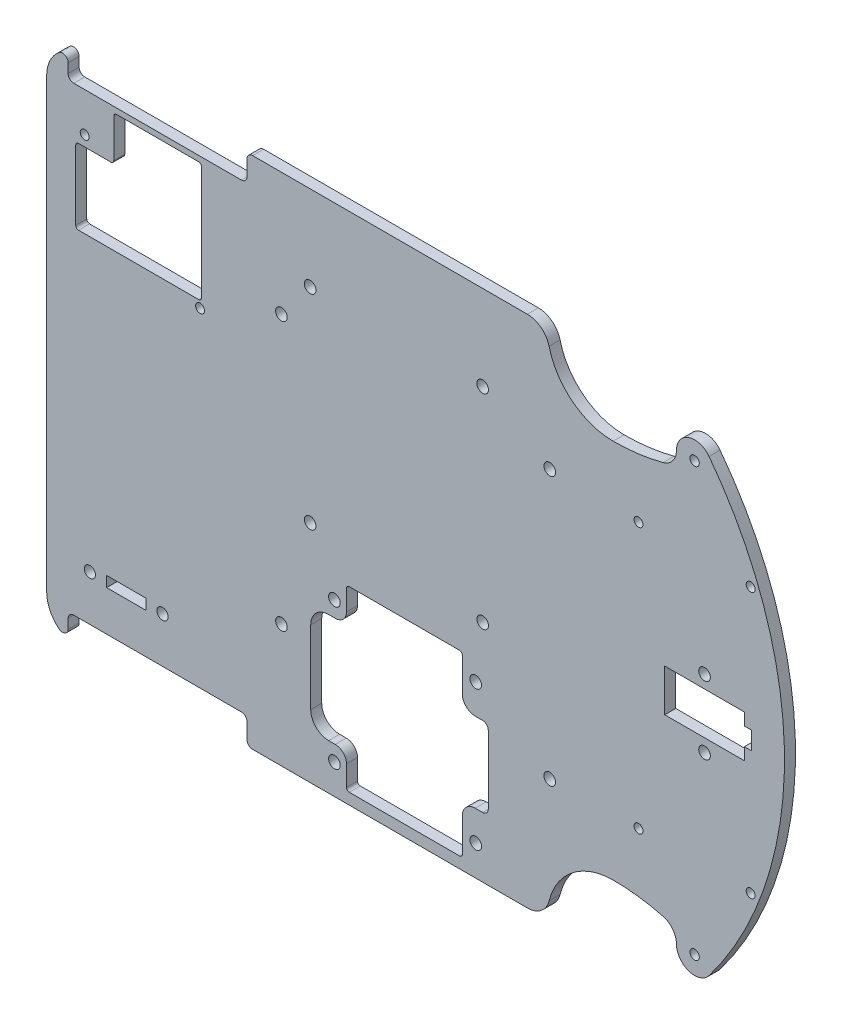
SolidWorks part; units mm, degrees
ref_plane "Alzado" through (0, 0, 0) normal (0, 0, 1) x (1, 0, 0)
ref_plane "Planta" through (0, 0, 0) normal (0, 1, 0) x (1, 0, 0)
ref_plane "Vista lateral" through (0, 0, 0) normal (1, 0, 0) x (0, 0, -1)
sketch "Croquis1" plane through (0, 0, 0) normal (0, 0, 1) x (1, 0, 0)
  line L1 (-104.775, -73.025) -> (104.775, -73.025)
  line L2 (-104.775, -73.025) -> (-104.775, 73.025)
  line L3 (-104.775, 73.025) -> (104.775, 73.025)
  line L4 (104.775, -73.025) -> (104.775, 73.025)
  line L5 (-104.775, -73.025) -> (104.775, 73.025) construction
  line L6 (-104.775, 73.025) -> (104.775, -73.025) construction
  point P0 (0, 0)
  dimension "D1" = 146.05
  dimension "D2" = 209.55
extrude "Saliente-Extruir1" add sketch "Croquis1" along normal blind 3.1242
sketch "Croquis2" plane through (0, 0, 3.1242) normal (0, 0, 1) x (1, 0, 0)
  line L0 (-104.775, -73.025) -> (104.775, -73.025) construction
  line L1 (104.775, 73.025) -> (43.634, 73.025)
  line L2 (104.775, 73.025) -> (104.775, -73.025)
  line L3 (104.775, -73.025) -> (43.634, -73.025)
  line L4 (43.634, 73.025) -> (43.634, -73.025)
  line L5 (0, 0) -> (104.775, 0) construction
  line L6 (69.7976, 73.025) -> (78.6114, 73.025)
  line L7 (69.7976, 73.025) -> (69.7976, 55.6514)
  line L8 (69.7976, 55.6514) -> (78.6114, 55.6514)
  line L9 (78.6114, 73.025) -> (78.6114, 55.6514)
  line L10 (78.6114, -73.025) -> (78.6114, -55.6514)
  line L11 (69.7976, -55.6514) -> (78.6114, -55.6514)
  line L12 (69.7976, -73.025) -> (69.7976, -55.6514)
  line L13 (69.7976, -73.025) -> (78.6114, -73.025)
  circle A0 centre (79.2464, 60.7314) radius 2.921
  circle A1 centre (79.2464, 60.7314) radius 1.3335
  circle A2 centre (79.2464, -60.7314) radius 1.3335
  circle A3 centre (79.2464, -60.7314) radius 2.921
  point P11 (74.2045, 73.025)
  point P12 (74.2045, 55.6514)
  point P13 (79.2464, 57.8104)
  point P14 (82.1674, 60.7314)
  point P28 (82.1674, -60.7314)
  point P29 (79.2464, -57.8104)
  point P30 (74.2045, -55.6514)
  point P31 (74.2045, -73.025)
  point P32 (79.2464, -59.3979)
  point P33 (79.2464, 59.3979)
  point P34 (79.2464, -62.0649)
  point P35 (79.2464, 62.0649)
  dimension "D3" = 5.842
  dimension "D4" = 1.5875
  dimension "D1" = 61.141
  dimension "D2" = 8.8138
  dimension "D5" = 3.556
  dimension "D6" = 17.3736
  dimension "D7" = 118.7958
  dimension "D8" = 118.7958
  dimension "D9" = 124.1298
extrude "Cortar-Extruir1" cut sketch "Croquis2" against normal through all contours L9 A1 | L9 A1 | A2
sketch "Croquis9" plane through (0, 0, 3.1242) normal (0, 0, 1) x (1, 0, 0)
  line L0 (63.3206, 37.6809) -> (95.1722, 37.6809) construction
  line L1 (0, 0) -> (104.775, 0) construction
  line L2 (104.775, -73.025) -> (104.775, 73.025) construction
  line L3 (63.3206, -37.6809) -> (95.1722, -37.6809) construction
  circle A0 centre (63.3206, 37.6809) radius 1.27
  circle A1 centre (95.1722, 37.6809) radius 1.27
  circle A2 centre (95.1722, 37.6809) radius 2.794
  circle A3 centre (79.2464, 60.7314) radius 1.3335 construction
  circle A4 centre (79.2464, 60.7314) radius 1.3335
  circle A5 centre (95.1722, -37.6809) radius 1.27
  circle A6 centre (63.3206, -37.6809) radius 1.27
  point P4 (79.2464, 62.0649)
  point P5 (95.1722, 34.8869)
  point P9 (79.2464, 37.6809)
  point P22 (95.1722, -34.8869)
  point P23 (64.5906, 37.6809)
  point P24 (93.9022, 37.6809)
  dimension "D1" = 29.3116
  dimension "D2" = 2.54
  dimension "D3" = 27.178
  dimension "D4" = 5.588
extrude "Cortar-Extruir6" cut sketch "Croquis9" against normal through all
sketch "Croquis3" plane through (0, 0, 3.1242) normal (0, 0, 1) x (1, 0, 0)
  line L0 (104.775, -73.025) -> (104.775, 73.025) construction
  line L1 (104.775, 73.025) -> (-104.775, 73.025) construction
  line L2 (0, 0) -> (104.775, 0) construction
  line L3 (38.1, 73.025) -> (74.087, 73.025)
  line L4 (38.1, 73.025) -> (38.1, 53.975)
  line L5 (38.1, 53.975) -> (74.087, 53.975)
  line L6 (74.087, 73.025) -> (74.087, 53.975)
  line L7 (74.087, -73.025) -> (74.087, -53.975)
  line L8 (38.1, -53.975) -> (74.087, -53.975)
  line L9 (38.1, -73.025) -> (38.1, -53.975)
  line L10 (38.1, -73.025) -> (74.087, -73.025)
  line L11 (-104.775, -73.025) -> (104.775, -73.025) construction
  line L12 (-95.25, 73.025) -> (0, 73.025)
  line L13 (-104.775, 63.5) -> (-104.775, -63.5)
  line L14 (-95.25, -73.025) -> (0, -73.025)
  line L15 (0, 73.025) -> (0, -73.025)
  circle A0 centre (79.2464, 60.7314) radius 5.1594
  arc A1 (83.3624, 63.8423) -> (83.3624, -63.8423) centre (-1.1052, 0) cw
  arc A2 (74.087, 60.7314) -> (70.3041, 55.8198) centre (69.007, 60.7314) cw
  arc A3 (31.75, 73.025) -> (38.1, 66.675) centre (31.75, 66.675) cw
  arc A4 (37.9138, 68.2015) -> (56.0935, 53.975) centre (56.0935, 72.704) ccw
  arc A5 (37.9138, -68.2015) -> (56.0935, -53.975) centre (56.0935, -72.704) cw
  arc A6 (31.75, -73.025) -> (38.1, -66.675) centre (31.75, -66.675) ccw
  arc A7 (70.3041, -55.8198) -> (56.0935, -53.975) centre (56.0935, -109.6304) ccw
  circle A8 centre (79.2464, -60.7314) radius 5.1594
  arc A9 (-104.775, -63.5) -> (-95.25, -73.025) centre (-95.25, -63.5) ccw
  arc A10 (-95.25, 73.025) -> (-104.775, 63.5) centre (-95.25, 63.5) ccw
  arc A11 (70.3041, 55.8198) -> (56.0935, 53.975) centre (56.0935, 109.6304) cw
  arc A12 (74.087, -60.7314) -> (70.3041, -55.8198) centre (69.007, -60.7314) ccw
  point P48 (-104.775, 73.025)
  point P51 (25.4, 69.2498)
  line M6 (104.775, -73.025) -> (104.775, 73.025)
  line M7 (104.775, 73.025) -> (-104.775, 73.025)
  line M8 (-104.775, 73.025) -> (-104.775, -73.025)
  line M9 (-104.775, -73.025) -> (104.775, -73.025)
  dimension "D1" = 19.05
  dimension "D3" = 6.35
  dimension "D4" = 9.525
  dimension "D5" = 10.3187
  dimension "D6" = 5.08
  dimension "D2" = 38.1
extrude "Cortar-Extruir2" cut sketch "Croquis3" against normal through all contours A3 A4 L4 M7 | A11 A2 L6 L4 A4 M7 | A0 A1 L6 M6 M7 | A1 A8 L7 M9 M6 | L7 A12 A7 A5 L9 M9 | A6 L9 A5 M9 | A10 M7 M8 | A9 M8 M9
sketch "Croquis5" plane through (0, 0, 3.1242) normal (0, 0, 1) x (1, 0, 0)
  line L0 (-95.25, -73.025) -> (31.75, -73.025) construction
  line L1 (-29.7815, -19.2786) -> (20.6375, -19.2786)
  line L2 (-29.7815, -19.2786) -> (-29.7815, -69.85)
  line L3 (-29.7815, -69.85) -> (20.6375, -69.85)
  line L4 (20.6375, -19.2786) -> (20.6375, -69.85)
  line L5 (-29.7815, -44.5643) -> (20.6375, -44.5643) construction
  line L6 (25.4, -63.5) -> (25.4, -62.2144) construction
  line L7 (20.6375, -69.85) -> (13.2715, -69.85)
  line L8 (20.6375, -69.85) -> (20.6375, -19.2786)
  line L9 (20.6375, -19.2786) -> (13.2715, -19.2786)
  line L10 (13.2715, -69.85) -> (13.2715, -19.2786)
  line L11 (-29.7815, -19.2786) -> (-19.6215, -19.2786)
  line L12 (-29.7815, -19.2786) -> (-29.7815, -69.85)
  line L13 (-29.7815, -69.85) -> (-19.6215, -69.85)
  line L14 (-19.6215, -19.2786) -> (-19.6215, -69.85)
  line L15 (13.2715, -33.2486) -> (20.6375, -33.2486)
  line L16 (13.2715, -33.2486) -> (13.2715, -55.88)
  line L17 (13.2715, -55.88) -> (20.6375, -55.88)
  line L18 (20.6375, -33.2486) -> (20.6375, -55.88)
  line L19 (-19.6215, -29.0576) -> (-29.7815, -29.0576)
  line L20 (-19.6215, -29.0576) -> (-19.6215, -60.071)
  line L21 (-19.6215, -60.071) -> (-29.7815, -60.071)
  line L22 (-29.7815, -29.0576) -> (-29.7815, -60.071)
  circle A0 centre (17.0815, -24.7396) radius 1.651
  circle A1 centre (-23.0505, -24.6126) radius 1.651
  circle A2 centre (17.0815, -64.389) radius 1.651
  circle A3 centre (-23.0505, -64.516) radius 1.651
  arc A4 (19.05, -55.88) -> (20.6375, -54.2925) centre (19.05, -54.2925) ccw
  arc A5 (16.9545, -55.88) -> (13.2715, -59.563) centre (16.9545, -59.563) ccw
  arc A6 (-24.7015, -60.071) -> (-29.7815, -54.991) centre (-24.7015, -54.991) cw
  arc A7 (-22.7965, -60.071) -> (-19.6215, -63.246) centre (-22.7965, -63.246) cw
  arc A8 (19.05, -33.2486) -> (20.6375, -34.8361) centre (19.05, -34.8361) cw
  arc A9 (16.9545, -33.2486) -> (13.2715, -29.5656) centre (16.9545, -29.5656) cw
  arc A10 (-24.7015, -29.0576) -> (-29.7815, -34.1376) centre (-24.7015, -34.1376) ccw
  arc A11 (-22.7965, -29.0576) -> (-19.6215, -25.8826) centre (-22.7965, -25.8826) ccw
  arc A12 (-19.6215, -20.0724) -> (-18.8278, -19.2786) centre (-18.8278, -20.0724) cw
  arc A13 (12.4777, -19.2786) -> (13.2715, -20.0724) centre (12.4777, -20.0724) cw
  arc A14 (12.4777, -69.85) -> (13.2715, -69.0563) centre (12.4777, -69.0563) ccw
  arc A15 (-19.6215, -69.0563) -> (-18.8278, -69.85) centre (-18.8278, -69.0563) ccw
  point P4 (18.7325, -24.7396)
  point P5 (17.0815, -23.0886)
  point P6 (-23.0505, -22.9616)
  point P14 (-24.7015, -24.6126)
  dimension "D5" = 3.302
  dimension "D16" = 1.5875
  dimension "D17" = 3.175
  dimension "D18" = 0.7937
  dimension "D1" = 50.5714
  dimension "D2" = 50.419
  dimension "D3" = 3.81
  dimension "D4" = 1.905
  dimension "D6" = 3.175
  dimension "D7" = 4.7625
  dimension "D8" = 5.08
  dimension "D9" = 3.683
  dimension "D10" = 7.366
  dimension "D11" = 10.16
  dimension "D12" = 13.97
  dimension "D13" = 13.97
  dimension "D14" = 9.779
  dimension "D15" = 9.779
extrude "Driver" cut sketch "Croquis5" against normal through all contours L22 L5 L14 L19 A10 | L5 L12 A6 L21 L20 | L14 L5 L16 L10 L1 | L16 L5 L18 A8 L15 | L5 L10 L17 A4 L8 | L5 L20 L14 L3 L10 | A5 L17 L10 | L21 A7 L14 | A11 L19 L14 | L15 A9 L10 | A1 | A3 | A2 | A0
sketch "Croquis6" plane through (0, 0, 3.1242) normal (0, 0, 1) x (1, 0, 0)
  line L0 (-33.45, 19.8814) -> (22.55, 19.8814)
  line L1 (-29.95, 48.8814) -> (19.05, 48.8814)
  line L2 (-29.95, 48.8814) -> (-29.95, -9.1186)
  line L3 (-29.95, -9.1186) -> (19.05, -9.1186)
  line L4 (19.05, 48.8814) -> (19.05, -9.1186)
  line L5 (-18.8278, -19.2786) -> (12.4777, -19.2786) construction
  line L6 (-5.45, -9.1186) -> (-5.45, 74.7014)
  circle A0 centre (-29.95, 48.8814) radius 1.651
  circle A1 centre (19.05, 48.8814) radius 1.651
  circle A2 centre (19.05, -9.1186) radius 1.651
  circle A3 centre (-29.95, -9.1186) radius 1.651
  point P13 (-5.45, 19.8814)
  point P14 (19.05, 19.8814)
  point P16 (-5.45, 48.8814)
  dimension "D1" = 3.302
  dimension "D2" = 58
  dimension "D3" = 49
  dimension "D4" = 56
  dimension "D5" = 6.35
  dimension "D6" = 10.16
  dimension "D7" = 83.82
extrude "RasPi" cut sketch "Croquis6" against normal through all contours A3 | A2 | A1 | A0
sketch "Croquis8" plane through (0, 0, 3.1242) normal (0, 0, 1) x (1, 0, 0)
  line L0 (-93.98, 54.3306) -> (-61.214, 28.0162)
  line L12 (-104.775, 63.5) -> (-104.775, -63.5) construction
  line L13 (-54.4614, 66.3702) -> (-54.4614, -66.3702) construction
  circle A0 centre (-93.98, 54.3306) radius 1.27
  circle A1 centre (-61.214, 28.0162) radius 1.27
  point P2 (-54.4614, 66.3702)
  point P8 (-61.214, 26.7462)
  point P9 (-93.98, 53.0606)
  point P10 (-95.25, 54.3306)
  point P12 (-59.944, 28.0162)
  point P14 (-54.4614, 0)
  dimension "D1" = 13.3096
  dimension "D3" = 2.54
  dimension "D4" = 2.54
  dimension "D2" = 32.766
  dimension "D5" = 9.525
  dimension "D6" = 39.624
  dimension "D7" = 132.7404
extrude "Diferencial trasero" cut sketch "Croquis8" against normal through all contours A0 | A1
sketch "Croquis7" plane through (0, 0, 3.1242) normal (0, 0, 1) x (1, 0, 0)
  line L0 (-82.1901, 33.7483) -> (-82.1901, -50.9778) construction
  line L1 (-87.7464, -50.9778) -> (-76.6339, -50.9778)
  line L2 (-87.7464, -50.9778) -> (-87.7464, -53.975)
  line L3 (-87.7464, -53.975) -> (-76.6339, -53.975)
  line L4 (-76.6339, -50.9778) -> (-76.6339, -53.975)
  line L5 (-95.885, 61.138) -> (-68.4952, 61.138)
  line L6 (-95.885, 61.138) -> (-95.885, 33.7483)
  line L7 (-95.885, 33.7483) -> (-68.4952, 33.7483)
  line L8 (-68.4952, 61.138) -> (-68.4952, 33.7483)
  line L9 (-95.25, -73.025) -> (31.75, -73.025) construction
  circle A0 centre (-71.8714, -52.4764) radius 1.5875
  circle A1 centre (-92.5089, -52.4764) radius 1.5875
  point P16 (-76.6339, -52.4764)
  point P20 (-87.7464, -52.4764)
  dimension "D4" = 3.175
  dimension "D1" = 2.9972
  dimension "D2" = 11.1125
  dimension "D3" = 19.05
  dimension "D5" = 4.7625
extrude "Cortar-Extruir7" cut sketch "Croquis7" against normal through all contours A1 | A0 | L3 L4 L1 L2
sketch "Croquis10" plane through (0, 0, 3.1242) normal (0, 0, 1) x (1, 0, 0)
  line L0 (-104.775, 63.5) -> (-104.775, -63.5) construction
  line L1 (61.3912, -19.4466) -> (54.8894, -19.4466)
  line L2 (61.3912, -19.4466) -> (61.3912, 12.2487)
  line L3 (61.3912, 12.2487) -> (54.8894, 12.2487)
  line L4 (54.8894, -19.4466) -> (54.8894, 12.2487)
  line L5 (61.3912, -19.4466) -> (54.8894, 12.2487) construction
  line L6 (61.3912, 12.2487) -> (54.8894, -19.4466) construction
  line L7 (82.0674, 9.652) -> (82.0674, -9.652) construction
  line L8 (70.7644, -5.9944) -> (93.3704, -5.9944)
  line L9 (70.7644, -5.9944) -> (70.7644, 5.9944)
  line L10 (70.7644, 5.9944) -> (93.3704, 5.9944)
  line L11 (93.3704, -5.9944) -> (93.3704, 5.9944)
  line L12 (70.7644, -5.9944) -> (93.3704, 5.9944) construction
  line L13 (70.7644, 5.9944) -> (93.3704, -5.9944) construction
  line L14 (93.3704, -5.9944) -> (93.3704, 5.9944)
  line L15 (93.3704, 3.1134) -> (93.3704, -1.9666)
  line L16 (82.0674, 9.652) -> (82.0674, -17.272) construction
  line L18 (93.3704, -2.54) -> (95.4024, -2.54)
  line L19 (93.3704, -2.54) -> (93.3704, 2.54)
  line L20 (93.3704, 2.54) -> (95.4024, 2.54)
  line L21 (95.4024, -2.54) -> (95.4024, 2.54)
  circle A0 centre (82.0674, 9.652) radius 1.651
  circle A1 centre (82.0674, -9.652) radius 1.651
  circle A2 centre (82.0674, 9.652) radius 1.651
  point P0 (58.1403, -3.599)
  point P16 (82.0674, 0)
  point P21 (93.3704, 0)
  point P26 (95.4024, 0)
  point P27 (0, 0)
  dimension "D5" = 3.302
  dimension "D1" = 159.6644
  dimension "D2" = 19.304
  dimension "D3" = 22.606
  dimension "D4" = 11.9888
  dimension "D6" = 26.924
  dimension "D7" = 175.5394
  dimension "D8" = 2.032
  dimension "D9" = 5.08
extrude "Cortar-Extruir10" cut sketch "Croquis10" against normal through all contours A0 | L8 L11 L14 L10 L9 | A1 | L18 L21 L20 L14
sketch "Croquis11" plane through (0, 0, 3.1242) normal (0, 0, 1) x (1, 0, 0)
  line L1 (-84.9313, 63.8302) -> (-61.6268, 63.8302)
  line L2 (-85.725, 63.0365) -> (-85.725, 29.9529)
  line L3 (-85.725, 29.9529) -> (-61.6268, 29.9529)
  line L4 (-60.833, 63.0365) -> (-60.833, 30.7467)
  line L5 (-60.833, 29.9529) -> (-95.7263, 29.953)
  line L6 (-60.833, 29.9529) -> (-60.833, 51.289)
  line L7 (-60.833, 51.289) -> (-95.7263, 51.2889)
  line L8 (-96.52, 30.7467) -> (-96.52, 50.4952)
  line L9 (-104.775, 63.5) -> (-104.775, -63.5) construction
  line L10 (31.75, 73.025) -> (-95.25, 73.025) construction
  line L11 (-95.25, 73.025) -> (-57.658, 73.025)
  line L12 (-95.25, 73.025) -> (-95.25, 65.4177)
  line L13 (-95.25, 65.4177) -> (-57.658, 65.4177)
  line L14 (-57.658, 73.025) -> (-57.658, 65.4177)
  line L15 (-46.2915, 73.025) -> (-47.879, 73.025)
  line L16 (-98.679, 80.6323) -> (-47.879, 80.6323)
  line L17 (-98.679, 80.6323) -> (-98.679, 67.0052)
  line L18 (-97.0915, 65.4177) -> (-49.4665, 65.4177)
  line L19 (-47.879, 80.6323) -> (-47.879, 67.0052)
  line L20 (-98.679, 80.6323) -> (-47.879, 65.4177) construction
  line L21 (-98.679, 65.4177) -> (-47.879, 80.6323) construction
  line L22 (0, 0) -> (-104.775, 0) construction
  line L23 (-98.679, -65.4177) -> (-47.879, -80.6323) construction
  line L24 (-98.679, -80.6323) -> (-47.879, -65.4177) construction
  line L25 (-47.879, -80.6323) -> (-47.879, -67.0052)
  line L26 (-97.0915, -65.4177) -> (-49.4665, -65.4177)
  line L27 (-98.679, -80.6323) -> (-98.679, -67.0052)
  line L28 (-98.679, -80.6323) -> (-47.879, -80.6323)
  line L29 (-46.2915, -73.025) -> (-47.879, -73.025)
  line L30 (-57.658, -73.025) -> (-57.658, -65.4177)
  line L31 (-95.25, -65.4177) -> (-57.658, -65.4177)
  line L32 (-95.25, -73.025) -> (-95.25, -65.4177)
  line L33 (-95.25, -73.025) -> (-57.658, -73.025)
  circle A0 centre (-61.214, 28.0162) radius 1.27 construction
  arc A1 (-95.7263, 29.953) -> (-96.52, 30.7467) centre (-95.7263, 30.7467) cw
  arc A2 (-95.7263, 51.2889) -> (-96.52, 50.4952) centre (-95.7263, 50.4952) ccw
  arc A3 (-61.6268, 29.9529) -> (-60.833, 30.7467) centre (-61.6268, 30.7467) ccw
  arc A4 (-61.6268, 63.8302) -> (-60.833, 63.0365) centre (-61.6268, 63.0365) cw
  arc A5 (-84.9313, 63.8302) -> (-85.725, 63.0365) centre (-84.9313, 63.0365) ccw
  arc A6 (-85.725, 52.0827) -> (-86.5188, 51.2889) centre (-86.5188, 52.0827) cw
  circle A7 centre (-93.98, 54.3306) radius 1.27 construction
  circle A8 centre (-93.98, 54.3306) radius 1.27
  arc A9 (-49.4665, 65.4177) -> (-47.879, 67.0052) centre (-49.4665, 67.0052) ccw
  arc A10 (-98.679, 67.0052) -> (-97.0915, 65.4177) centre (-97.0915, 67.0052) ccw
  arc A11 (-47.879, 71.4375) -> (-46.2915, 73.025) centre (-46.2915, 71.4375) cw
  arc A12 (-101.2698, 70.8816) -> (-98.679, 69.6513) centre (-100.2665, 69.6513) cw
  arc A13 (-95.25, 73.025) -> (-104.775, 63.5) centre (-95.25, 63.5) ccw construction
  arc A14 (-95.25, 73.025) -> (-104.775, 63.5) centre (-95.25, 63.5) ccw
  arc A15 (-95.25, -73.025) -> (-104.775, -63.5) centre (-95.25, -63.5) cw
  arc A16 (-101.2698, -70.8816) -> (-98.679, -69.6513) centre (-100.2665, -69.6513) ccw
  arc A17 (-47.879, -71.4375) -> (-46.2915, -73.025) centre (-46.2915, -71.4375) ccw
  arc A18 (-98.679, -67.0052) -> (-97.0915, -65.4177) centre (-97.0915, -67.0052) cw
  arc A19 (-49.4665, -65.4177) -> (-47.879, -67.0052) centre (-49.4665, -67.0052) cw
  point P11 (-61.214, 29.2862)
  point P16 (-96.52, 29.953)
  point P19 (-96.52, 51.2889)
  point P37 (-95.25, 54.3306)
  point P38 (-73.279, 73.025)
  point P46 (-73.279, 63.8302)
  point P91 (-73.279, -73.025)
  dimension "D8" = 0.7937
  dimension "D9" = 1.5875
  dimension "D4" = 3.0417
  dimension "D11" = 50.8
  dimension "D12" = 1.5875
  dimension "D1" = 9.4996
  dimension "D2" = 2.54
  dimension "D3" = 19.05
  dimension "D5" = 21.336
  dimension "D6" = 24.892
  dimension "D7" = 0.6668
  dimension "D10" = 3.175
extrude "Cortar-Extruir11" cut sketch "Croquis11" against normal through all contours L1 A5 L2 L7 L4 A4 | L3 A3 L4 L7 L2 | L7 A2 L8 A1 L5 L2 | L2 A6 L7 | L17 A10 L18 L12 L11 L14 A9 L19 L16 | L14 L11 L12 L13 | L19 A11 L15 | L12 A14 L17 A10 L18 | L17 A14 A12 | A16 A15 L27 | A18 L27 A15 L32 L26 | L32 L33 L30 L26 | A19 L26 L30 L33 A15 L27 L28 L25 | A17 L25 L29
sketch "Croquis12" plane through (0, 0, 3.1242) normal (0, 0, 1) x (1, 0, 0)
  line L1 (-38.1, -38.1) -> (38.1, -38.1)
  line L2 (-38.1, -38.1) -> (-38.1, 38.1)
  line L3 (-38.1, 38.1) -> (38.1, 38.1)
  line L4 (38.1, -38.1) -> (38.1, 38.1)
  line L5 (-38.1, -38.1) -> (38.1, 38.1) construction
  line L6 (-38.1, 38.1) -> (38.1, -38.1) construction
  circle A2 centre (38.1, 38.1) radius 1.651
  circle A3 centre (-38.1, 38.1) radius 1.651
  circle A4 centre (-38.1, -38.1) radius 1.651
  circle A5 centre (38.1, -38.1) radius 1.651
  point P0 (0, 0)
  dimension "D1" = 3.302
  dimension "D2" = 76.2
  dimension "D3" = 76.2
extrude "Cortar-Extruir12" cut sketch "Croquis12" against normal through all contours A3 | A2 | A5 | A4
